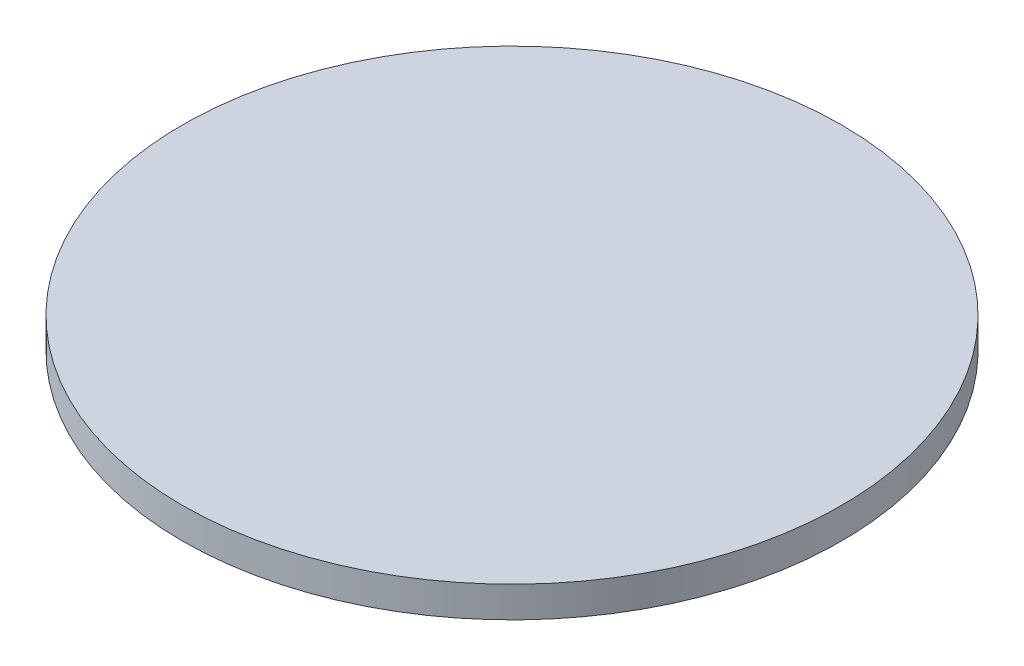
SolidWorks part; units mm, degrees
ref_plane "Front Plane" through (0, 0, 0) normal (0, 0, 1) x (1, 0, 0)
ref_plane "Top Plane" through (0, 0, 0) normal (0, 1, 0) x (1, 0, 0)
ref_plane "Right Plane" through (0, 0, 0) normal (1, 0, 0) x (0, 0, -1)
sketch "Sketch1" plane through (0, 0, 0) normal (0, 1, 0) x (1, 0, 0)
  circle A0 centre (8.8155, 5.8295) radius 32
extrude "Boss-Extrude1" add sketch "Sketch1" along normal blind 3
